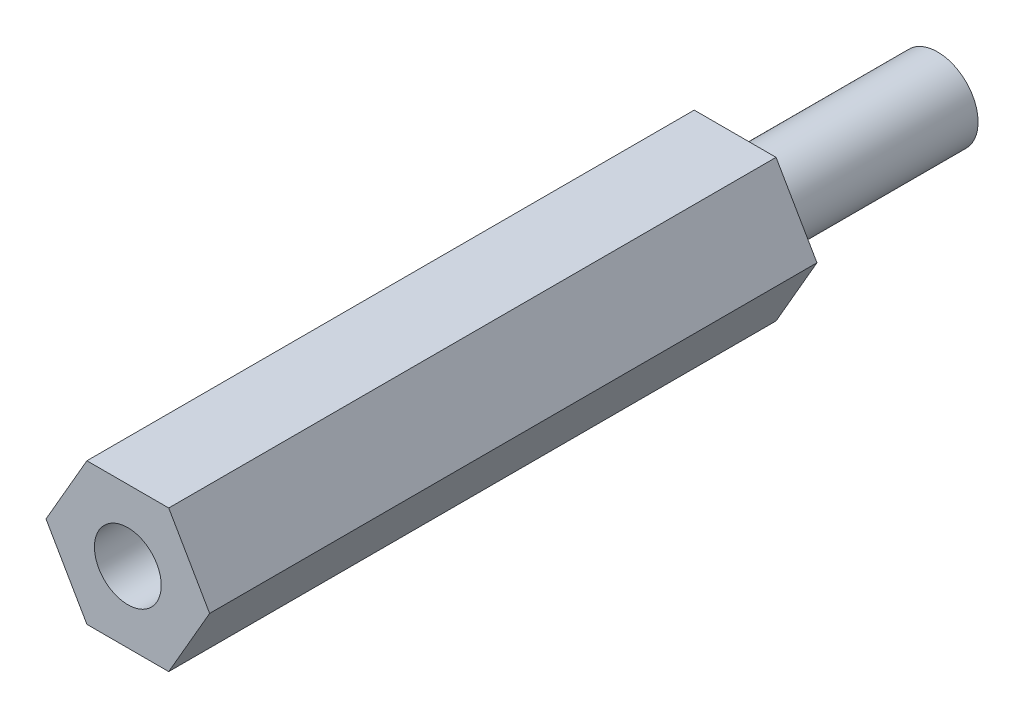
SolidWorks part; units mm, degrees
material "黃銅"
ref_plane "前基準面" through (0, 0, 0) normal (0, 0, 1) x (1, 0, 0)
ref_plane "上基準面" through (0, 0, 0) normal (0, 1, 0) x (1, 0, 0)
ref_plane "右基準面" through (0, 0, 0) normal (1, 0, 0) x (0, 0, -1)
sketch "草圖1" plane through (0, 0, 0) normal (0, 0, 1) x (1, 0, 0)
  line L1 (-2.0207, 3.5) -> (-4.0415, 0)
  line L2 (-4.0415, 0) -> (-2.0207, -3.5)
  line L3 (-2.0207, -3.5) -> (2.0207, -3.5)
  line L4 (2.0207, -3.5) -> (4.0415, 0)
  line L5 (4.0415, 0) -> (2.0207, 3.5)
  line L6 (2.0207, 3.5) -> (-2.0207, 3.5)
  circle A0 centre (0, 0) radius 3.5 construction
  dimension "D1" = 7
extrude "填料-伸長1" add sketch "草圖1" along normal blind 30
sketch "草圖4" plane through (0, 0, 0) normal (0, 0, -1) x (-1, 0, 0)
  circle A0 centre (0, 0) radius 2
  dimension "D1" = 4
extrude "填料-伸長2" add sketch "草圖4" along normal blind 10
hole_wizard "M4x0.7 螺紋孔1" positions "草圖2" profile "草圖3" tap size "M4x0.7" standard "Ansi Metric"
sketch "草圖2" plane through (0, 0, 30) normal (0, 0, 1) x (1, 0, 0)
  point P0 (0, 0)
sketch "草圖3" plane through (0, 0, 30) normal (1, 0, 0) x (0, -1, 0)
  line L0 (0, 0) -> (0, 11.0914)
  line L1 (0, 11.0914) -> (1.65, 10.1)
  line L2 (1.65, 10.1) -> (1.65, 0)
  line L5 (1.65, 0) -> (0, 0)
  line L10 (0, 11.0914) -> (-1.65, 10.1) construction
  line L11 (0, -6.35) -> (0, 107.95) construction
  dimension "螺孔鑽直徑" = 3.3
  dimension "螺孔鑽深度" = 10.1
  dimension "導頭角度" = 118
